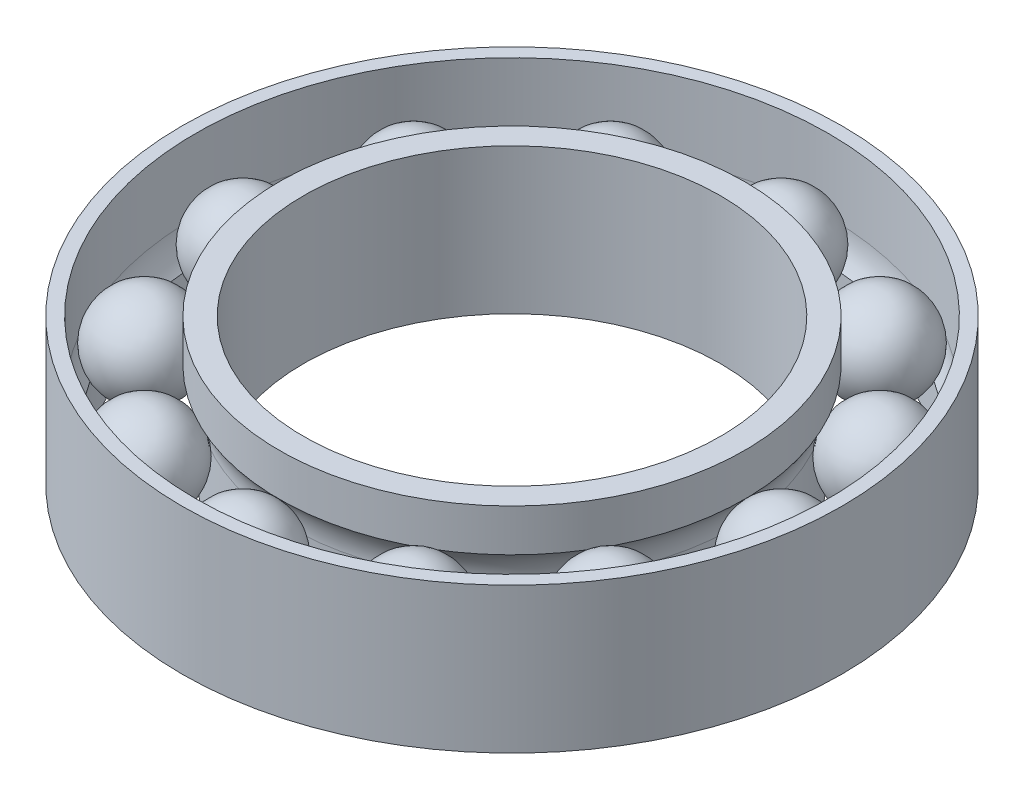
SolidWorks part; units mm, degrees
ref_plane "Front Plane" through (0, 0, 0) normal (0, 0, 1) x (1, 0, 0)
ref_plane "Top Plane" through (0, 0, 0) normal (0, 1, 0) x (1, 0, 0)
ref_plane "Right Plane" through (0, 0, 0) normal (1, 0, 0) x (0, 0, -1)
sketch "Sketch1" plane through (0, 0, 0) normal (0, 0, 1) x (1, 0, 0)
  line L0 (0, 3) -> (0, 16.0907) construction
  line L1 (4.3, 0) -> (4.575, 0)
  line L2 (6.8, 0) -> (6.8, 3)
  line L3 (6.8, 3) -> (6.525, 3)
  line L5 (4.3, 3) -> (4.3, 0)
  line L6 (0, 3) -> (0, -0.9619) construction
  line L7 (4.8, 3) -> (4.8, 2.1279)
  line L8 (6.3, 0.8819) -> (6.3, 0)
  line L9 (4.575, 1.5049) -> (4.575, 0)
  line L10 (6.525, 1.5049) -> (6.525, 3)
  line L11 (4.8, 3) -> (4.3, 3)
  line L12 (6.3, 0) -> (6.8, 0)
  arc A0 (4.8, 2.1279) -> (4.575, 1.5049) centre (5.55, 1.5049) ccw
  arc A1 (6.3, 0.8819) -> (6.525, 1.5049) centre (5.55, 1.5049) ccw
  dimension "D6" = 1.95
  dimension "D1" = 3
  dimension "D2" = 13.6
  dimension "D3" = 8.6
  dimension "D4" = 0.5
  dimension "D5" = 0.5
  dimension "D7" = 0.275
revolve "Revolve1" add sketch "Sketch1" angle 360 about L0
sketch "Sketch2" plane through (0, 0, 0) normal (0, 0, 1) x (1, 0, 0)
  line L0 (5.55, 2.475) -> (5.55, 0.525)
  line L2 (5.55, 0.2439) -> (5.55, 4.0723) construction
  arc A0 (5.55, 0.525) -> (5.55, 2.475) centre (5.55, 1.5) ccw
  dimension "D2" = 1.95
revolve "Revolve2" add sketch "Sketch2" angle 360 about L2
pattern_circular "CirPattern1" count 12 over 360 about axis through (0, 0, 0) along (0, 1, 0) of bodies 103
